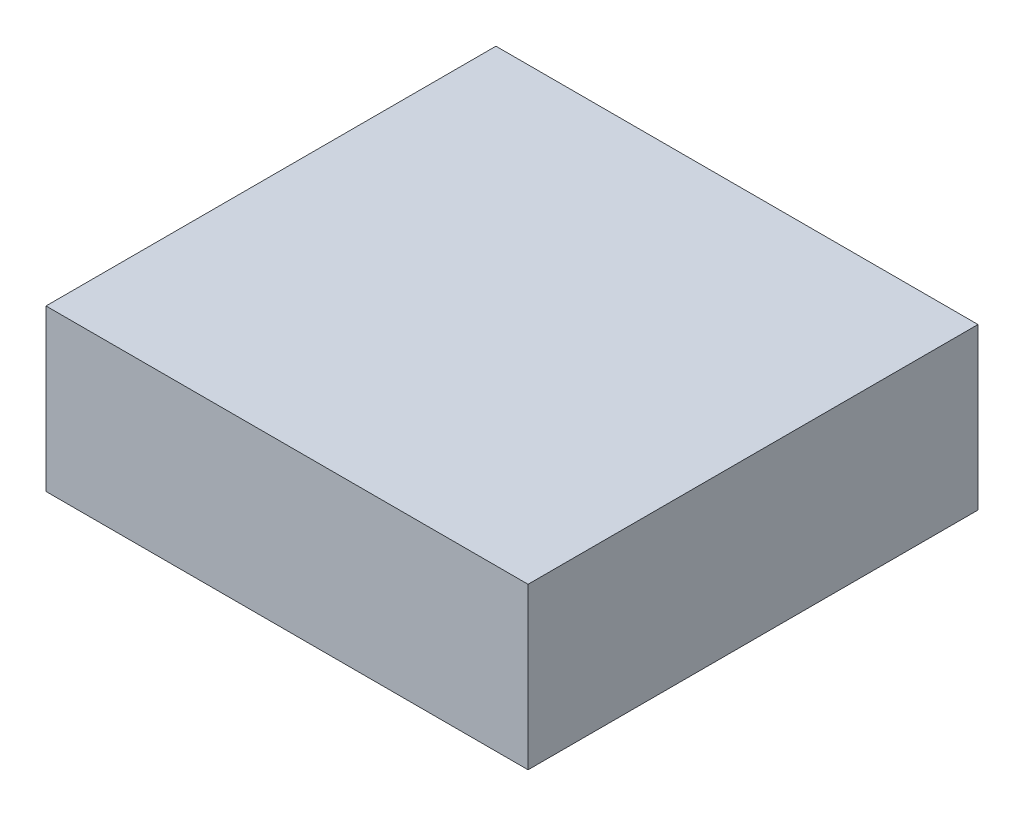
SolidWorks part; units mm, degrees
ref_plane "Front Plane" through (0, 0, 0) normal (0, 0, 1) x (1, 0, 0)
ref_plane "Top Plane" through (0, 0, 0) normal (0, 1, 0) x (1, 0, 0)
ref_plane "Right Plane" through (0, 0, 0) normal (1, 0, 0) x (0, 0, -1)
sketch "Sketch1" plane through (0, 0, 0) normal (0, 1, 0) x (1, 0, 0)
  line L1 (-227.25, -212.1) -> (227.25, -212.1)
  line L2 (-227.25, -212.1) -> (-227.25, 212.1)
  line L3 (-227.25, 212.1) -> (227.25, 212.1)
  line L4 (227.25, -212.1) -> (227.25, 212.1)
  line L5 (-227.25, -212.1) -> (227.25, 212.1) construction
  line L6 (-227.25, 212.1) -> (227.25, -212.1) construction
  point P0 (0, 0)
  dimension "D1" = 424.2
  dimension "D2" = 454.5
extrude "Boss-Extrude1" add sketch "Sketch1" along normal blind 151.5
sketch "Sketch3" plane through (0, 151.5, 0) normal (0, 1, 0) x (1, 0, 0)
  line L0 (0, 212.1) -> (0, -212.1)
  line L1 (-227.25, -212.1) -> (227.25, -212.1) construction
  line L2 (227.25, 0) -> (-227.25, 0)
  line L3 (-227.25, 212.1) -> (-227.25, -212.1) construction
  line L4 (227.25, -22) -> (-227.25, -22)
  line L5 (227.25, -44) -> (-227.25, -44)
  line L6 (227.25, 22) -> (-227.25, 22)
  line L7 (227.25, 44) -> (-227.25, 44)
  line L8 (227.25, 66) -> (-227.25, 66)
  line L9 (227.25, 88) -> (-227.25, 88)
  line L10 (227.25, 110) -> (-227.25, 110)
  line L11 (227.25, 132) -> (-227.25, 132)
  line L12 (227.25, 154) -> (-227.25, 154)
  line L13 (227.25, 176) -> (-227.25, 176)
  line L14 (227.25, 198) -> (-227.25, 198)
  line L15 (227.25, -66) -> (-227.25, -66)
  line L16 (227.25, -88) -> (-227.25, -88)
  line L17 (227.25, -110) -> (-227.25, -110)
  line L18 (227.25, -132) -> (-227.25, -132)
  line L19 (227.25, -154) -> (-227.25, -154)
  line L20 (227.25, -176) -> (-227.25, -176)
  line L21 (227.25, -198) -> (-227.25, -198)
  line L22 (23.7, 212.1) -> (23.7, -212.1)
  line L23 (47.4, 212.1) -> (47.4, -212.1)
  line L24 (71.1, 212.1) -> (71.1, -212.1)
  line L25 (94.8, 212.1) -> (94.8, -212.1)
  line L26 (118.5, 212.1) -> (118.5, -212.1)
  line L27 (142.2, 212.1) -> (142.2, -212.1)
  line L28 (165.9, 212.1) -> (165.9, -212.1)
  line L29 (189.6, 212.1) -> (189.6, -212.1)
  line L30 (213.3, 212.1) -> (213.3, -212.1)
  line L31 (-23.7, 212.1) -> (-23.7, -212.1)
  line L32 (-47.4, 212.1) -> (-47.4, -212.1)
  line L33 (-71.1, 212.1) -> (-71.1, -212.1)
  line L34 (-94.8, 212.1) -> (-94.8, -212.1)
  line L35 (-118.5, 212.1) -> (-118.5, -212.1)
  line L36 (-142.2, 212.1) -> (-142.2, -212.1)
  line L37 (-165.9, 212.1) -> (-165.9, -212.1)
  line L38 (-189.6, 212.1) -> (-189.6, -212.1)
  line L39 (-213.3, 212.1) -> (-213.3, -212.1)
  point P6 (0, 0)
  point P11 (0, 0)
  dimension "D1" = 90
  dimension "D4" = 22
  dimension "D5" = 22
  dimension "D8" = 23.7
  dimension "D9" = 23.7
  dimension "D2" = 10
  dimension "D3" = 10
  dimension "D6" = 10
  dimension "D7" = 10
